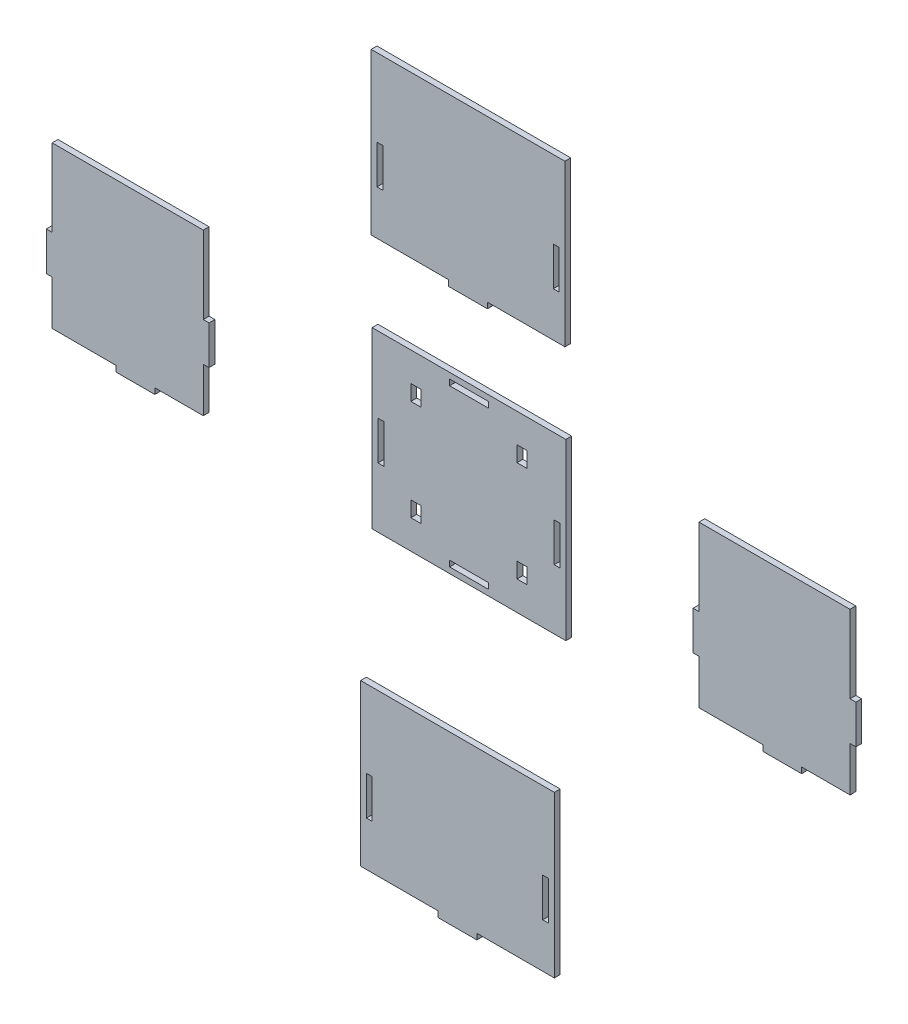
SolidWorks part; units mm, degrees
ref_plane "Спереди" through (0, 0, 0) normal (0, 0, 1) x (1, 0, 0)
ref_plane "Сверху" through (0, 0, 0) normal (0, 1, 0) x (1, 0, 0)
ref_plane "Справа" through (0, 0, 0) normal (1, 0, 0) x (0, 0, -1)
sketch "Эскиз1" plane through (0, 0, 0) normal (0, 0, 1) x (1, 0, 0)
  line L0 (-79.4238, 85.3283) -> (-79.4238, 82.3283)
  line L1 (-118.934, 44.1878) -> (-18.934, 44.1878)
  line L2 (-118.934, 44.1878) -> (-118.934, -45.8122)
  line L3 (-118.934, -45.8122) -> (-18.934, -45.8122)
  line L4 (-18.934, 44.1878) -> (-18.934, -45.8122)
  line L5 (-78.934, 41.1878) -> (-58.934, 41.1878)
  line L6 (-78.934, 41.1878) -> (-78.934, 38.1878)
  line L7 (-78.934, 38.1878) -> (-58.934, 38.1878)
  line L8 (-58.934, 41.1878) -> (-58.934, 38.1878)
  line L9 (-115.934, 5.1878) -> (-112.934, 5.1878)
  line L10 (-115.934, 5.1878) -> (-115.934, -14.8122)
  line L11 (-115.934, -14.8122) -> (-112.934, -14.8122)
  line L12 (-112.934, 5.1878) -> (-112.934, -14.8122)
  line L13 (-78.934, -42.8122) -> (-58.934, -42.8122)
  line L14 (-78.934, -42.8122) -> (-78.934, -39.8122)
  line L15 (-78.934, -39.8122) -> (-58.934, -39.8122)
  line L16 (-58.934, -42.8122) -> (-58.934, -39.8122)
  line L17 (-24.934, 5.1878) -> (-21.934, 5.1878)
  line L18 (-24.934, 5.1878) -> (-24.934, -14.8122)
  line L19 (-24.934, -14.8122) -> (-21.934, -14.8122)
  line L20 (-21.934, 5.1878) -> (-21.934, -14.8122)
  line L21 (-119.4238, 168.3283) -> (-19.4238, 168.3283)
  line L22 (-119.4238, 168.3283) -> (-119.4238, 85.3283)
  line L23 (-119.4238, 85.3283) -> (-79.4238, 85.3283)
  line L24 (-19.4238, 168.3283) -> (-19.4238, 85.3283)
  line L25 (-79.4238, 82.3283) -> (-59.4238, 82.3283)
  line L26 (-59.4238, 82.3283) -> (-59.4238, 85.3283)
  line L27 (-59.4238, 85.3283) -> (-19.4238, 85.3283)
  line L28 (-116.4238, 128.3283) -> (-113.4238, 128.3283)
  line L29 (-116.4238, 128.3283) -> (-116.4238, 108.3283)
  line L30 (-116.4238, 108.3283) -> (-113.4238, 108.3283)
  line L31 (-113.4238, 128.3283) -> (-113.4238, 108.3283)
  line L32 (-22.4238, 128.3283) -> (-25.4238, 128.3283)
  line L33 (-22.4238, 128.3283) -> (-22.4238, 108.3283)
  line L34 (-22.4238, 108.3283) -> (-25.4238, 108.3283)
  line L35 (-25.4238, 128.3283) -> (-25.4238, 108.3283)
  line L36 (-284.1137, 44.1878) -> (-206.1137, 44.1878)
  line L37 (-206.1137, 44.1878) -> (-206.1137, 4.1878)
  line L38 (-206.1137, 4.1878) -> (-203.1137, 4.1878)
  line L39 (-203.1137, 4.1878) -> (-203.1137, -15.8122)
  line L40 (-203.1137, -15.8122) -> (-206.1137, -15.8122)
  line L41 (-206.1137, -15.8122) -> (-206.1137, -38.8122)
  line L42 (-206.1137, -38.8122) -> (-231.1137, -38.8122)
  line L43 (-231.1137, -38.8122) -> (-231.1137, -41.8122)
  line L44 (-231.1137, -41.8122) -> (-251.1137, -41.8122)
  line L45 (-251.1137, -41.8122) -> (-251.1137, -38.8122)
  line L46 (-251.1137, -38.8122) -> (-284.1137, -38.8122)
  line L47 (-284.1137, -38.8122) -> (-284.1137, -15.8122)
  line L48 (-284.1137, -15.8122) -> (-287.1137, -15.8122)
  line L49 (-287.1137, -15.8122) -> (-287.1137, 4.1878)
  line L50 (-287.1137, 4.1878) -> (-284.1137, 4.1878)
  line L51 (-284.1137, 4.1878) -> (-284.1137, 44.1878)
  line L52 (-124.8731, -116.5648) -> (-24.8731, -116.5648)
  line L53 (-24.8731, -116.5648) -> (-24.8731, -199.5648)
  line L54 (-24.8731, -199.5648) -> (-64.8731, -199.5648)
  line L55 (-64.8731, -199.5648) -> (-64.8731, -202.5648)
  line L56 (-64.8731, -202.5648) -> (-84.8731, -202.5648)
  line L57 (-84.8731, -202.5648) -> (-84.8731, -199.5648)
  line L58 (-84.8731, -199.5648) -> (-124.8731, -199.5648)
  line L59 (-124.8731, -199.5648) -> (-124.8731, -116.5648)
  line L61 (-121.8731, -156.5648) -> (-118.8731, -156.5648)
  line L62 (-121.8731, -156.5648) -> (-121.8731, -176.5648)
  line L63 (-121.8731, -176.5648) -> (-118.8731, -176.5648)
  line L64 (-118.8731, -156.5648) -> (-118.8731, -176.5648)
  line L65 (-30.8731, -156.5648) -> (-27.8731, -156.5648)
  line L66 (-30.8731, -156.5648) -> (-30.8731, -176.5648)
  line L67 (-30.8731, -176.5648) -> (-27.8731, -176.5648)
  line L68 (-27.8731, -156.5648) -> (-27.8731, -176.5648)
  line L84 (-68.934, -1055.8122) -> (-68.934, 48944.1878) construction
  line L85 (-98.934, -22.8122) -> (-93.734, -22.8122)
  line L86 (-98.934, -22.8122) -> (-98.934, -30.8122)
  line L87 (-98.934, -30.8122) -> (-93.734, -30.8122)
  line L88 (-93.734, -22.8122) -> (-93.734, -30.8122)
  line L89 (-98.934, 29.1878) -> (-93.734, 29.1878)
  line L90 (-98.934, 29.1878) -> (-98.934, 21.1878)
  line L91 (-98.934, 21.1878) -> (-93.734, 21.1878)
  line L92 (-93.734, 29.1878) -> (-93.734, 21.1878)
  line L93 (-38.934, -30.8122) -> (-44.134, -30.8122)
  line L94 (-44.134, -22.8122) -> (-44.134, -30.8122)
  line L95 (-38.934, -22.8122) -> (-38.934, -30.8122)
  line L96 (-38.934, -22.8122) -> (-44.134, -22.8122)
  line L97 (-44.134, 29.1878) -> (-44.134, 21.1878)
  line L98 (-38.934, 21.1878) -> (-44.134, 21.1878)
  line L99 (-38.934, 29.1878) -> (-38.934, 21.1878)
  line L100 (-38.934, 29.1878) -> (-44.134, 29.1878)
  line L101 (49.774, 41.5859) -> (127.774, 41.5859)
  line L102 (127.774, 41.5859) -> (127.774, 1.5859)
  line L103 (127.774, 1.5859) -> (130.774, 1.5859)
  line L104 (130.774, 1.5859) -> (130.774, -18.4141)
  line L105 (130.774, -18.4141) -> (127.774, -18.4141)
  line L106 (127.774, -18.4141) -> (127.774, -41.4141)
  line L107 (127.774, -41.4141) -> (102.774, -41.4141)
  line L108 (102.774, -41.4141) -> (102.774, -44.4141)
  line L109 (102.774, -44.4141) -> (82.774, -44.4141)
  line L110 (82.774, -44.4141) -> (82.774, -41.4141)
  line L111 (82.774, -41.4141) -> (49.774, -41.4141)
  line L112 (49.774, -41.4141) -> (49.774, -18.4141)
  line L113 (49.774, -18.4141) -> (46.774, -18.4141)
  line L114 (46.774, -18.4141) -> (46.774, 1.5859)
  line L115 (46.774, 1.5859) -> (49.774, 1.5859)
  line L116 (49.774, 1.5859) -> (49.774, 41.5859)
  point P95 (-68.934, -45.8122)
  dimension "D1" = 90
  dimension "D2" = 100
  dimension "D3" = 3
  dimension "D4" = 3
  dimension "D5" = 20
  dimension "D6" = 20
  dimension "D7" = 3
  dimension "D8" = 3
  dimension "D9" = 20
  dimension "D10" = 3
  dimension "D11" = 3
  dimension "D12" = 20
  dimension "D13" = 3
  dimension "D14" = 3
  dimension "D15" = 40
  dimension "D16" = 31
  dimension "D17" = 31
  dimension "D18" = 40
  dimension "D19" = 100
  dimension "D20" = 86
  dimension "D21" = 3
  dimension "D22" = 20
  dimension "D23" = 3
  dimension "D24" = 40
  dimension "D25" = 40
  dimension "D26" = 3
  dimension "D27" = 3
  dimension "D28" = 20
  dimension "D29" = 40
  dimension "D30" = 20
  dimension "D31" = 3
  dimension "D32" = 78
  dimension "D33" = 20
  dimension "D34" = 86
  dimension "D35" = 3
  dimension "D36" = 3
  dimension "D37" = 20
  dimension "D38" = 3
  dimension "D39" = 3
  dimension "D40" = 3
  dimension "D41" = 3
  dimension "D42" = 20
  dimension "D43" = 40
  dimension "D44" = 40
  dimension "D45" = 25
  dimension "D46" = 3
  dimension "D47" = 3
  dimension "D48" = 20
  dimension "D49" = 3
  dimension "D50" = 3
  dimension "D51" = 3
  dimension "D52" = 3
  dimension "D53" = 20
  dimension "D54" = 40
  dimension "D55" = 40
  dimension "D56" = 25
  dimension "D59" = 100
  dimension "D60" = 86
  dimension "D61" = 3
  dimension "D62" = 3
  dimension "D63" = 3
  dimension "D64" = 3
  dimension "D65" = 20
  dimension "D66" = 20
  dimension "D67" = 3
  dimension "D68" = 3
  dimension "D69" = 40
  dimension "D70" = 40
  dimension "D71" = 20
  dimension "D72" = 40
  dimension "D73" = 5.2
  dimension "D74" = 5.2
  dimension "D75" = 8
  dimension "D76" = 8
  dimension "D77" = 15
  dimension "D78" = 15
  dimension "D79" = 20
  dimension "D80" = 20
extrude "Бобышка-Вытянуть1" add sketch "Эскиз1" along normal blind 3
